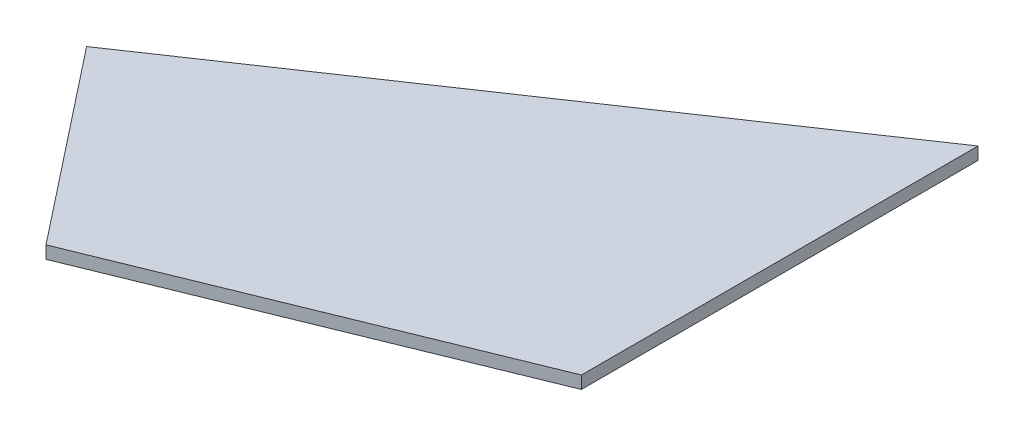
SolidWorks part; units mm, degrees
ref_plane "Plan de face" through (0, 0, 0) normal (0, 0, 1) x (1, 0, 0)
ref_plane "Plan de dessus" through (0, 0, 0) normal (0, 1, 0) x (1, 0, 0)
ref_plane "Plan de droite" through (0, 0, 0) normal (1, 0, 0) x (0, 0, -1)
sketch "Esquisse1" plane through (0, 0, 0) normal (0, 1, 0) x (1, 0, 0)
  line L0 (60.5952, 87.8676) -> (-24.1275, 30.5926)
  line L1 (-24.1275, 30.5926) -> (0, 0)
  line L2 (0, 0) -> (60.5952, 24.6907)
  line L3 (60.5952, 24.6907) -> (60.5952, 87.8676)
  point P4 (0, 0)
extrude "Boss.-Extru.1" add sketch "Esquisse1" along normal blind 2
